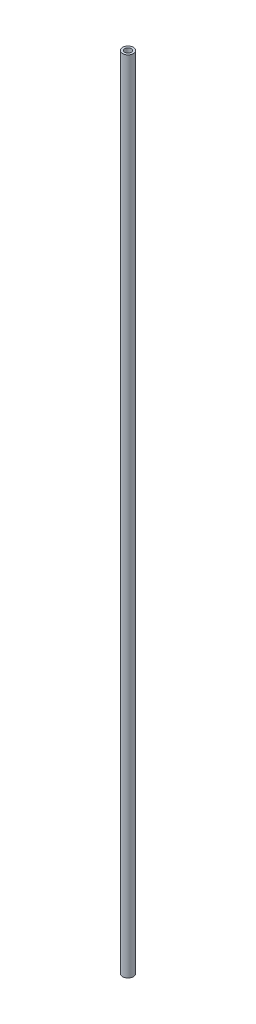
SolidWorks part; units mm, degrees
material "Thornel Mat VMA"
ref_plane "Front Plane" through (0, 0, 0) normal (0, 0, 1) x (1, 0, 0)
ref_plane "Top Plane" through (0, 0, 0) normal (0, 1, 0) x (1, 0, 0)
ref_plane "Right Plane" through (0, 0, 0) normal (1, 0, 0) x (0, 0, -1)
sketch "Sketch1" plane through (0, 0, 0) normal (0, 1, 0) x (1, 0, 0)
  circle A0 centre (0, 0) radius 6.223
  circle A2 centre (0, 0) radius 3.683
  dimension "D1" = 12.446
  dimension "D2" = 2.54
extrude "Boss-Extrude1" add sketch "Sketch1" along normal mid plane 914.4
